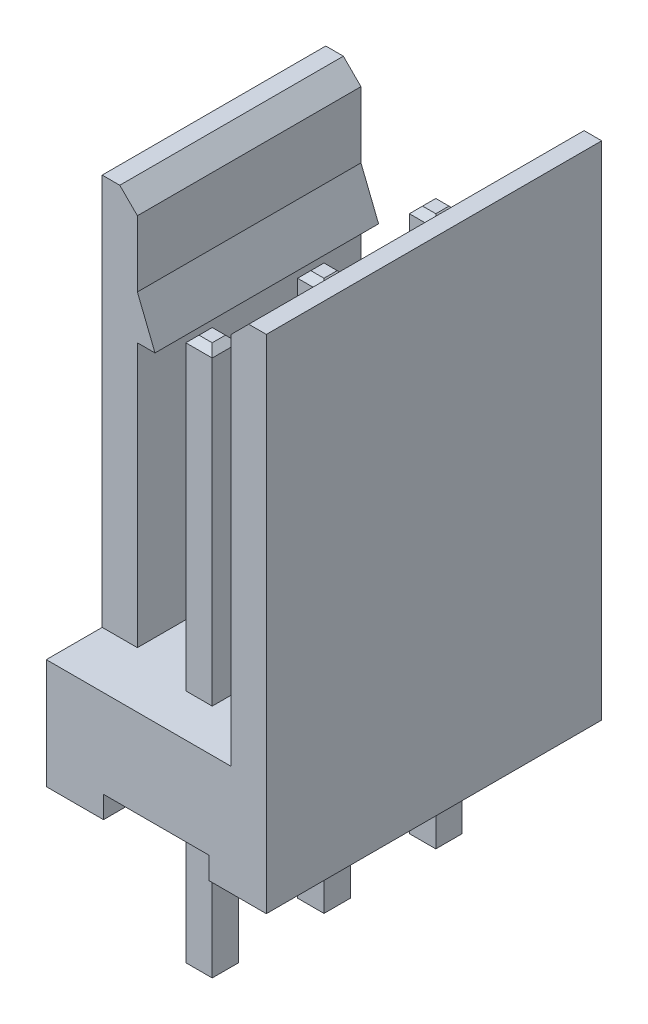
SolidWorks part; units mm, degrees
ref_plane "Plan de face" through (0, 0, 0) normal (0, 0, 1) x (1, 0, 0)
ref_plane "Plan de dessus" through (0, 0, 0) normal (0, 1, 0) x (1, 0, 0)
ref_plane "Plan de droite" through (0, 0, 0) normal (1, 0, 0) x (0, 0, -1)
sketch "Esquisse1" plane through (0, 0, 0) normal (0, 0, 1) x (1, 0, 0)
  line L0 (0, 11.4) -> (0, 0)
  line L1 (0, 0) -> (5, 0)
  line L2 (5, 0) -> (5, 11.4)
  line L3 (5, 11.4) -> (4.2, 11.4)
  line L4 (4.2, 11.4) -> (4.2, 2.5)
  line L5 (4.2, 2.5) -> (0.8, 2.5)
  line L6 (0.8, 2.5) -> (0.8, 11.4)
  line L10 (0.8, 11.4) -> (0, 11.4)
  dimension "D1" = 2.5
  dimension "D2" = 5
  dimension "D3" = 11.4
  dimension "D4" = 0.8
  dimension "D5" = 0.8
extrude "Boss.-Extru.1" add sketch "Esquisse1" along normal blind 7.62
sketch "Esquisse3" plane through (0, 11.4, 0) normal (0, 1, 0) x (1, 0, 0)
  line L0 (0.8, -7.62) -> (0.8, 0) construction
  line L1 (0, 0) -> (0.8, 0)
  line L2 (0, 0) -> (0, -1.27)
  line L3 (0, -1.27) -> (0.8, -1.27)
  line L4 (0.8, 0) -> (0.8, -1.27)
  line L6 (0, -7.62) -> (0.8, -7.62)
  line L7 (0, -7.62) -> (0, -6.35)
  line L8 (0, -6.35) -> (0.8, -6.35)
  line L9 (0.8, -7.62) -> (0.8, -6.35)
  dimension "D1" = 1.27
extrude "Enlèv. mat.-Extru.1" cut sketch "Esquisse3" against normal up to surface (8.9 mm away) up to face at (2.5, 2.5, 3.81)
sketch "Esquisse4" plane through (0, 0, 7.62) normal (0, 0, 1) x (1, 0, 0)
  line L0 (0, 0) -> (5, 0) construction
  line L1 (1.3, 0) -> (3.7, 0)
  line L2 (1.3, 0) -> (1.3, 0.5)
  line L3 (1.3, 0.5) -> (3.7, 0.5)
  line L4 (3.7, 0) -> (3.7, 0.5)
  line L5 (0, 2.5) -> (0, 0) construction
  line L6 (5, 0) -> (5, 11.4) construction
  point P8 (0, 1.25)
  dimension "D1" = 0.5
  dimension "D2" = 1.3
  dimension "D3" = 1.3
extrude "Enlèv. mat.-Extru.2" cut sketch "Esquisse4" against normal through all
sketch "Esquisse2" plane through (0, 0.5, 0) normal (0, -1, 0) x (1, 0, 0)
  line L0 (2.5, 6.35) -> (2.5, 7.62) construction
  line L1 (2.2, 6.05) -> (2.8, 6.05)
  line L2 (2.2, 6.05) -> (2.2, 6.65)
  line L3 (2.2, 6.65) -> (2.8, 6.65)
  line L4 (2.8, 6.05) -> (2.8, 6.65)
  line L5 (2.2, 6.05) -> (2.8, 6.65) construction
  line L6 (2.2, 6.65) -> (2.8, 6.05) construction
  line L7 (2.2, 0.97) -> (2.8, 0.97)
  line L8 (2.2, 0.97) -> (2.2, 1.57)
  line L9 (2.2, 1.57) -> (2.8, 1.57)
  line L10 (2.8, 0.97) -> (2.8, 1.57)
  line L11 (2.2, 0.97) -> (2.8, 1.57) construction
  line L12 (2.2, 1.57) -> (2.8, 0.97) construction
  line L13 (2.5, 6.35) -> (2.5, 3.81) construction
  line L16 (2.5, 1.27) -> (2.5, 0) construction
  line L18 (3.7, 7.62) -> (1.3, 7.62) construction
  line L19 (3.7, 0) -> (1.3, 0) construction
  line L29 (2.2, 4.11) -> (2.8, 4.11)
  line L30 (2.2, 4.11) -> (2.2, 3.51)
  line L31 (2.2, 3.51) -> (2.8, 3.51)
  line L32 (2.8, 4.11) -> (2.8, 3.51)
  line L33 (2.2, 4.11) -> (2.8, 3.51) construction
  line L34 (2.2, 3.51) -> (2.8, 4.11) construction
  line L37 (2.5, 3.81) -> (2.5, 1.27) construction
  point P0 (2.5, 6.35)
  point P5 (2.5, 1.27)
  point P12 (2.5, 3.8306)
  point P16 (2.5492, 5.08)
  point P28 (2.5, 3.81)
  dimension "D1" = 0.6
  dimension "D2" = 2.54
extrude "Boss.-Extru.2" add sketch "Esquisse2" along normal blind 3.5 and the other way blind 9
sketch "Esquisse5" plane through (0, 0, 6.35) normal (0, 0, 1) x (1, 0, 0)
  line L0 (0.8, 9.5) -> (1.2, 8.5)
  line L1 (0.8, 2.5) -> (0.8, 11.4) construction
  line L2 (1.2, 8.5) -> (0.8, 8.5)
  line L3 (0.8, 8.5) -> (0.8, 9.5)
  line L4 (2.8, 9.5) -> (2.2, 9.5) construction
  dimension "D1" = 1
  dimension "D2" = 0.4
extrude "Boss.-Extru.3" add sketch "Esquisse5" against normal up to surface (5.08 mm away) up to face at (0.4, 6.95, 1.27)
chamfer "Chanfrein4" distance 0.15 angle 45 24 edges at (2.5, -3, 6.05) (2.2, -3, 6.35) (2.5, -3, 6.65) (2.8, -3, 6.35) (2.5, -3, 0.97) (2.2, -3, 1.27) (2.5, -3, 1.57) (2.8, -3, 1.27) (2.5, 9.5, 6.65) (2.2, 9.5, 6.35) (2.5, 9.5, 6.05) (2.8, 9.5, 6.35) (2.5, 9.5, 1.57) (2.2, 9.5, 1.27) (2.5, 9.5, 0.97) (2.8, 9.5, 1.27) (2.5, -3, 3.51) (2.2, -3, 3.81) (2.5, -3, 4.11) (2.8, -3, 3.81) (2.5, 9.5, 4.11) (2.2, 9.5, 3.81) (2.5, 9.5, 3.51) (2.8, 9.5, 3.81)
chamfer "Chanfrein5" distance 0.4 angle 45 2 edges at (4.2, 11.4, 3.81) (0.8, 11.4, 3.81)
